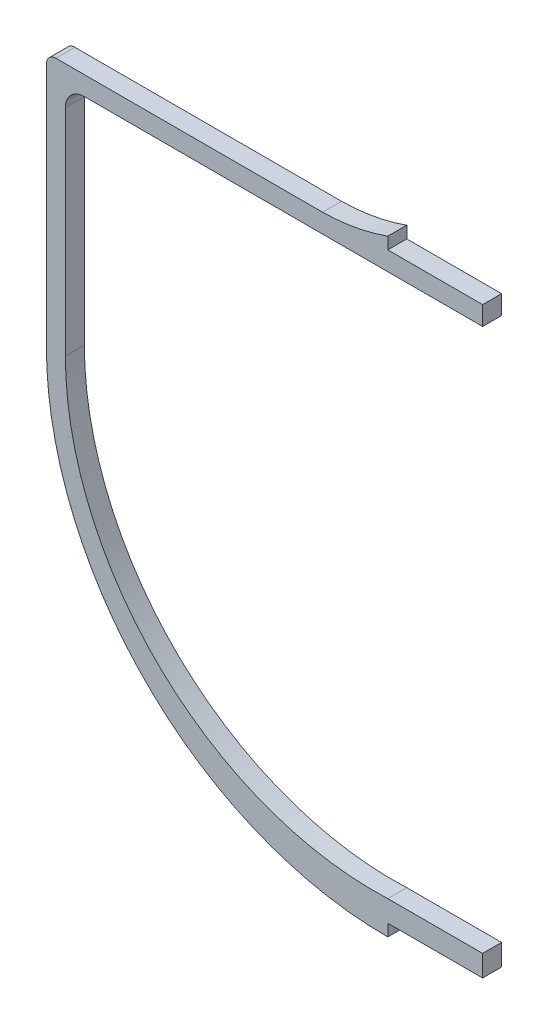
SolidWorks part; units mm, degrees
ref_plane "Front Plane" through (0, 0, 0) normal (0, 0, 1) x (1, 0, 0)
ref_plane "Top Plane" through (0, 0, 0) normal (0, 1, 0) x (1, 0, 0)
ref_plane "Right Plane" through (0, 0, 0) normal (1, 0, 0) x (0, 0, -1)
sketch "Sketch1" plane through (0, 0, 0) normal (0, 0, 1) x (1, 0, 0)
  line L0 (0, 0) -> (0, 128) construction
  line L1 (0, 128) -> (-68, 128) construction
  line L2 (-68, 128) -> (-68, 70) construction
  line L3 (0, 0) -> (0, 2.5)
  line L4 (-68, 125.5) -> (-13.7523, 125.5)
  line L6 (-68, 121.5) -> (20, 121.5)
  line L7 (20, 125.5) -> (20, 121.5)
  line L8 (-68, 125.5) -> (-72, 125.5)
  line L9 (-68, 121.5) -> (-68, 72.0942)
  line L11 (-72, 125.5) -> (-72, 72.0942)
  line L12 (0, 2.5) -> (20, 2.5)
  line L13 (20, 2.5) -> (20, 7)
  line L14 (20, 7) -> (0, 7)
  line L15 (0, 128) -> (0, 125.5)
  line L16 (0, 125.5) -> (20, 125.5)
  arc A1 (-72, 72.0942) -> (0, 0) centre (-0.2744, 71.726) ccw
  arc A2 (-68, 72.0942) -> (0, 7) centre (-2.8437, 72.0942) ccw
  arc A3 (0, 128) -> (-13.7523, 125.5) centre (-14.3762, 168.0069) cw
  point P10 (20, 123.5)
  dimension "D1" = 128
  dimension "D9" = 7
  dimension "D2" = 68
  dimension "D3" = 58
  dimension "D4" = 4
  dimension "D5" = 88
  dimension "D6" = 20
  dimension "D7" = 2.5
  dimension "D8" = 4
  dimension "D10" = 2.5
  dimension "D11" = 20
extrude "Boss-Extrude1" add sketch "Sketch1" along normal blind 4
fillet "Fillet1" radius 4 1 edges at (-68, 121.5, 2)
fillet "Fillet2" radius 2 1 edges at (-72, 125.5, 2)
